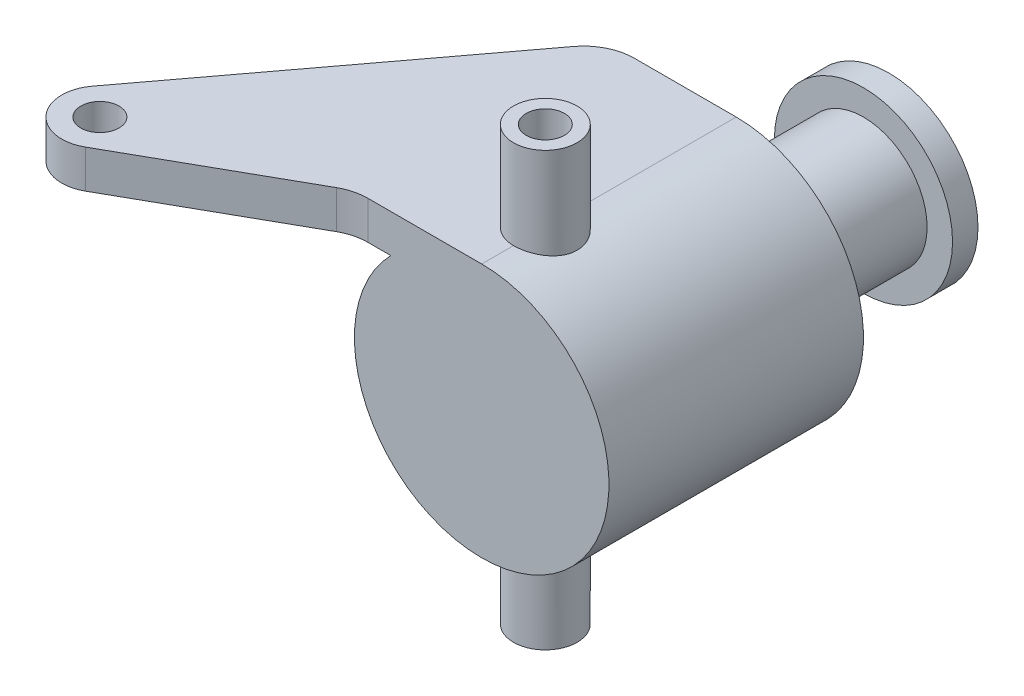
SolidWorks part; units mm, degrees
material "1060 Alloy"
ref_plane "Front Plane" through (0, 0, 0) normal (0, 0, 1) x (1, 0, 0)
ref_plane "Top Plane" through (0, 0, 0) normal (0, 1, 0) x (1, 0, 0)
ref_plane "Right Plane" through (0, 0, 0) normal (1, 0, 0) x (0, 0, -1)
sketch "Sketch1" plane through (0, 0, 0) normal (0, 0, 1) x (1, 0, 0)
  circle A0 centre (0, 0) radius 12.7
  dimension "D2" = 25.4
extrude "Boss-Extrude1" add sketch "Sketch1" along normal mid plane 25.4
ref_plane "Plane1" through (0, 12.7, 0) normal (0, 1, 0) x (1, 0, 0)
sketch "Sketch2" plane through (0, 12.7, 0) normal (0, 1, 0) x (1, 0, 0)
  line L0 (0, 12.7) -> (0, -12.7)
  line L2 (-12.7, -12.7) -> (12.7, -12.7) construction
  line L3 (0, -12.7) -> (-11.3686, -12.7)
  line L4 (-13.8603, -13.353) -> (-29.8813, -22.3702)
  line L5 (-34.798, -16.764) -> (-14.224, 10.668)
  line L6 (-10.16, 12.7) -> (0, 12.7)
  line L7 (-12.7, 12.7) -> (-12.7, -12.7) construction
  line L8 (-12.7, 12.7) -> (-12.7, -12.7) construction
  arc A0 (-29.8813, -22.3702) -> (-34.798, -16.764) centre (-31.75, -19.05) cw
  circle A1 centre (-31.75, -19.05) radius 1.905
  arc A2 (-13.8603, -13.353) -> (-11.3686, -12.7) centre (-11.3686, -17.78) cw
  arc A3 (-10.16, 12.7) -> (-14.224, 10.668) centre (-10.16, 7.62) ccw
  dimension "D3" = 3.81
  dimension "D4" = 3.81
  dimension "D5" = 5.08
  dimension "D1" = 19.05
  dimension "D2" = 31.75
extrude "Boss-Extrude2" add sketch "Sketch2" against normal blind 3.81
sketch "Sketch3" plane through (0, 0, -12.7) normal (0, 0, -1) x (-1, 0, 0)
  circle A0 centre (0, 0) radius 6.35
  dimension "D1" = 12.7
extrude "Boss-Extrude3" add sketch "Sketch3" along normal blind 12.7
sketch "Sketch4" plane through (0, 0, -25.4) normal (0, 0, -1) x (-1, 0, 0)
  circle A2 centre (0, 0) radius 6.35 construction
  circle A3 centre (0, 0) radius 6.35 construction
  circle A4 centre (0, 0) radius 8.89
  dimension "D1" = 2.54
extrude "Boss-Extrude4" add sketch "Sketch4" along normal blind 2.54
sketch "Sketch5" plane through (0, 0, 0) normal (0, 1, 0) x (1, 0, 0)
  line L1 (0, -12.7) -> (0, 12.7) construction
  circle A0 centre (0, -6.35) radius 3.175
  dimension "D2" = 6.35
  dimension "D1" = 6.35
extrude "Boss-Extrude5" add sketch "Sketch5" along normal mid plane 43.18
sketch "Sketch6" plane through (0, 0, 0) normal (0, 1, 0) x (1, 0, 0)
  circle A0 centre (0, -6.35) radius 1.905
  circle A1 centre (0, -6.35) radius 3.175
  circle A2 centre (0, -6.35) radius 3.175 construction
  dimension "D2" = 3.81
  dimension "D1" = 0
extrude "Cut-Extrude1" cut sketch "Sketch6" against normal through all both and the other way through all
sketch "Sketch7" plane through (0, 21.59, 0) normal (0, 1, 0) x (1, 0, 0)
  circle A0 centre (0, -6.35) radius 3.175 construction
  circle A1 centre (0, -6.35) radius 3.175
ref_point "rot_origin"
